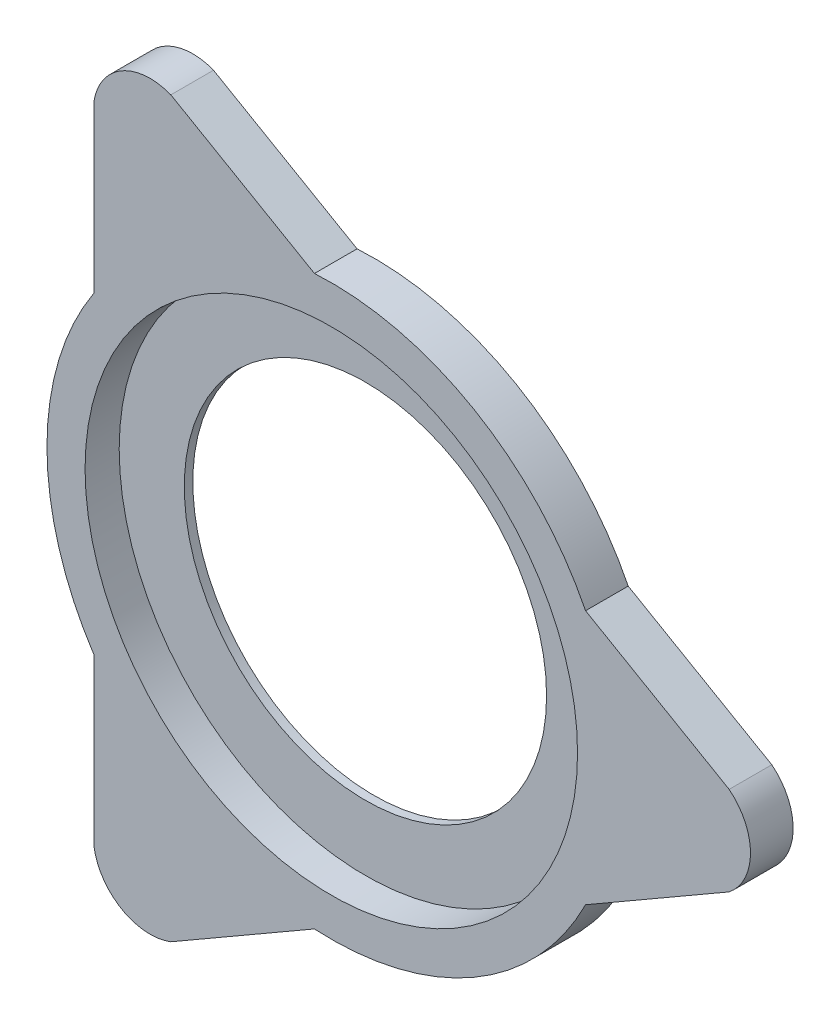
SolidWorks part; units mm, degrees
ref_plane "Front" through (0, 0, 0) normal (0, 0, 1) x (1, 0, 0)
ref_plane "Top" through (0, 0, 0) normal (0, 1, 0) x (1, 0, 0)
ref_plane "Right" through (0, 0, 0) normal (1, 0, 0) x (0, 0, -1)
sketch "Sketch1" plane through (0, 0, 0) normal (0, 0, 1) x (1, 0, 0)
  line L0 (88.8452, -9.918) -> (56.7796, -28.4311)
  line L1 (80.9128, 0) -> (-40.4564, 70.0725) construction
  line L2 (-40.4564, 70.0725) -> (-40.4564, -70.0725) construction
  line L3 (-40.4564, -70.0725) -> (80.9128, 0) construction
  line L4 (88.8452, 9.918) -> (56.7796, 28.4311)
  line L5 (-53.0118, 71.9832) -> (-53.0118, 34.957)
  line L6 (-3.7678, -63.3881) -> (-35.8334, -81.9012)
  line L7 (-53.0118, -34.957) -> (-53.0118, -71.9832)
  line L8 (-3.7678, 63.3881) -> (-35.8334, 81.9012)
  arc A0 (56.7796, 28.4311) -> (-3.7678, 63.3881) centre (0, 0) ccw
  circle A1 centre (0, 0) radius 40.4564
  arc A2 (-53.0118, 71.9832) -> (-35.8334, 81.9012) centre (-40.4564, 70.0725) cw
  arc A3 (88.8452, 9.918) -> (88.8452, -9.918) centre (80.9128, 0) cw
  arc A4 (-35.8334, -81.9012) -> (-53.0118, -71.9832) centre (-40.4564, -70.0725) cw
  arc A5 (-53.0118, 34.957) -> (-53.0118, -34.957) centre (0, 0) ccw
  arc A6 (-3.7678, -63.3881) -> (56.7796, -28.4311) centre (0, 0) ccw
  dimension "D1" = 63.5
  dimension "D3" = 12.7
extrude "Base-Extrude" add sketch "Sketch1" along normal blind 9.525
sketch "Sketch2" plane through (0, 0, 9.525) normal (0, 0, 1) x (1, 0, 0)
  circle A0 centre (0, 0) radius 54.9919
  arc A1 (56.7796, 28.4311) -> (-3.7678, 63.3881) centre (0, 0) ccw construction
extrude "Cut-Extrude1" cut sketch "Sketch2" against normal blind 7.62
